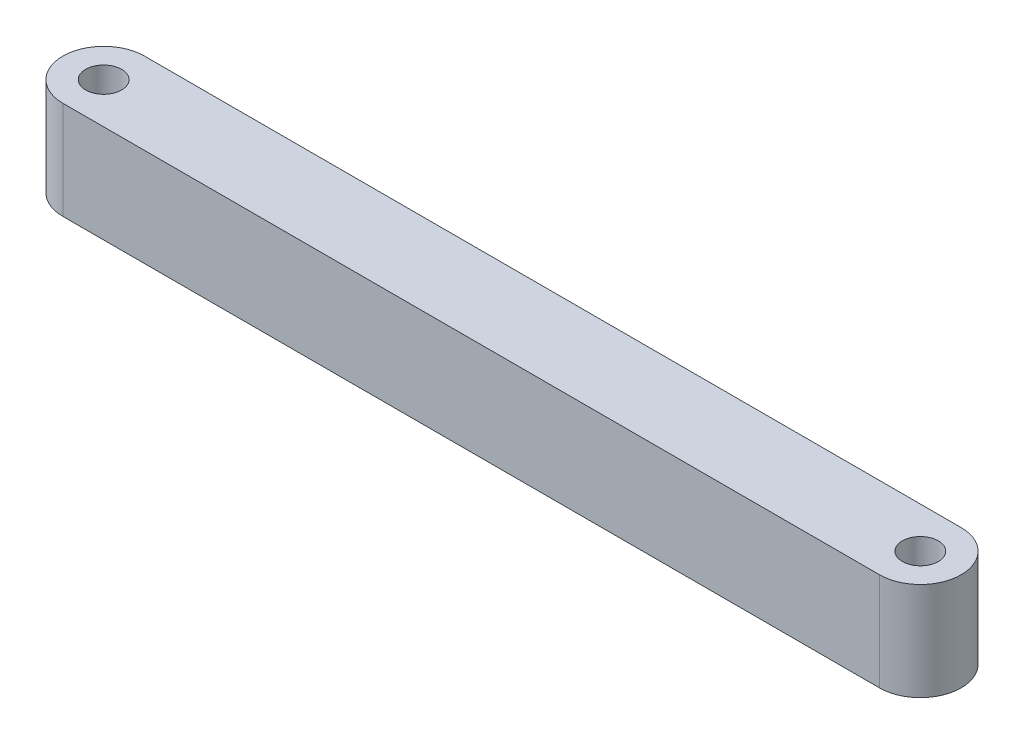
SolidWorks part; units mm, degrees
ref_plane "Front Plane" through (0, 0, 0) normal (0, 0, 1) x (1, 0, 0)
ref_plane "Top Plane" through (0, 0, 0) normal (0, 1, 0) x (1, 0, 0)
ref_plane "Right Plane" through (0, 0, 0) normal (1, 0, 0) x (0, 0, -1)
sketch "Sketch1" plane through (0, 0, 0) normal (0, 1, 0) x (1, 0, 0)
  line L0 (-6.5355, -1.4191) -> (38.4645, -1.4191) construction
  line L1 (-6.5355, 3.5809) -> (83.4645, 3.5809)
  line L3 (-6.5355, -6.4191) -> (83.4645, -6.4191)
  line L5 (93.4645, 3.5809) -> (83.4645, 3.5809)
  line L6 (38.4645, 3.5809) -> (38.4645, -6.4191) construction
  line L7 (91.2645, -1.4191) -> (93.4645, -1.4191) construction
  line L8 (93.4645, -6.4191) -> (83.4645, -6.4191)
  arc A0 (-6.5355, 3.5809) -> (-6.5355, -6.4191) centre (-6.5355, -1.4191) ccw
  circle A2 centre (-6.5355, -1.4191) radius 2.2
  circle A3 centre (93.4645, -1.4191) radius 2.2
  arc A4 (93.4645, -6.4191) -> (93.4645, 3.5809) centre (93.4645, -1.4191) ccw
  circle A5 centre (-6.5355, -1.4191) radius 5
  circle A6 centre (93.4645, -1.4191) radius 5
  dimension "D1" = 100
extrude "Boss-Extrude1" add sketch "Sketch1" along normal blind 12
